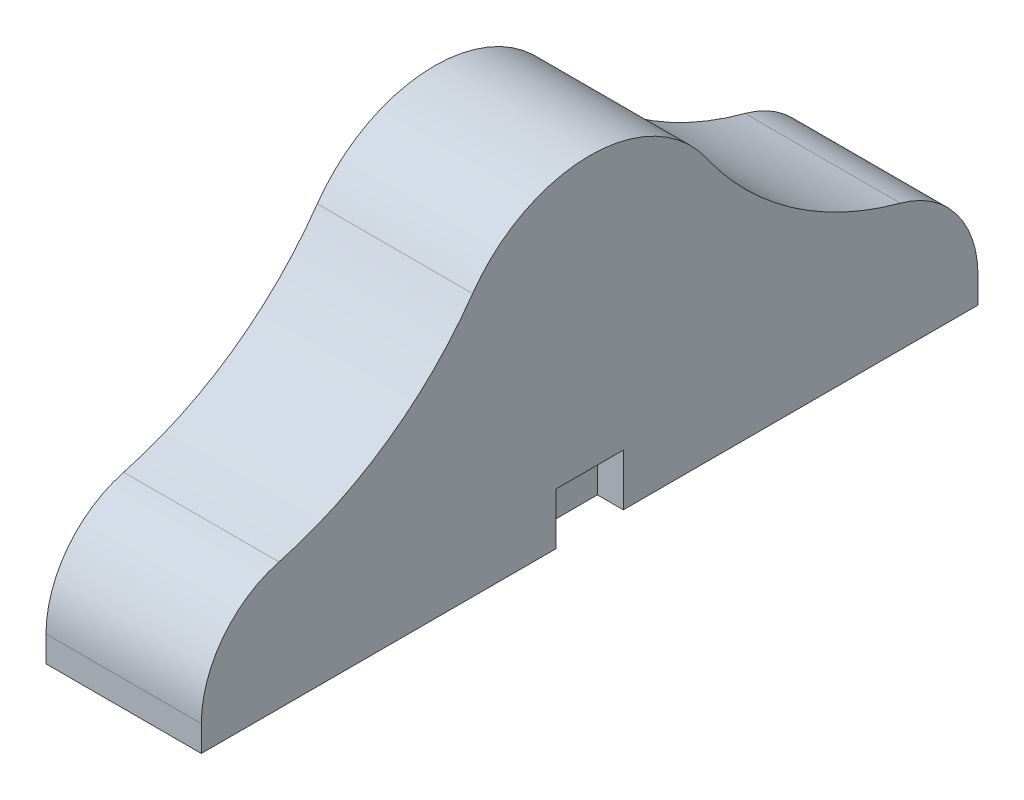
SolidWorks part; units mm, degrees
ref_plane "Front Plane" through (0, 0, 0) normal (0, 0, 1) x (1, 0, 0)
ref_plane "Top Plane" through (0, 0, 0) normal (0, 1, 0) x (1, 0, 0)
ref_plane "Right Plane" through (0, 0, 0) normal (1, 0, 0) x (0, 0, -1)
sketch "Sketch1" plane through (0, 0, 0) normal (1, 0, 0) x (0, 0, -1)
  line L0 (0, 0) -> (60, 0)
  line L1 (60, 0) -> (60, 2)
  line L2 (0, 0) -> (0, 2)
  line L3 (30, 0) -> (30, 27.8113) construction
  line L4 (30, 13.9616) -> (18.336, 22.1288) construction
  line L5 (-4.7429, 6.9408) -> (16.2966, 12.5783) construction
  line L6 (0, 2) -> (27.4, 2) construction
  line L7 (27.4, 2) -> (32.6, 2)
  line L8 (27.4, 2) -> (27.4, 4)
  line L9 (27.4, 4) -> (32.6, 4)
  line L10 (32.6, 2) -> (32.6, 4)
  arc A0 (20.9579, 20.293) -> (39.0421, 20.293) centre (30, 13.9616) cw
  arc A1 (0, 2) -> (6, 9.8194) centre (8.0952, 2) cw
  arc A2 (6, 9.8194) -> (20.9579, 20.293) centre (-0.9091, 35.6044) ccw
  arc A3 (60, 2) -> (54, 9.8194) centre (51.9048, 2) ccw
  arc A4 (54, 9.8194) -> (39.0421, 20.293) centre (60.9091, 35.6044) cw
  point P11 (30, 25)
  point P18 (30, 4)
  dimension "D1" = 55
  dimension "D2" = 15
  dimension "D3" = 60
  dimension "D4" = 2
  dimension "D5" = 6
  dimension "D6" = 25
  dimension "D7" = 5.2
  dimension "D8" = 2
extrude "Boss-Extrude1" add sketch "Sketch1" against normal blind 10
sketch "Sketch2" plane through (0, 0, 0) normal (1, 0, 0) x (0, 0, -1)
  line L0 (0, 0) -> (27.4, 0)
  line L1 (0, 0) -> (60, 0) construction
  line L2 (27.4, 0) -> (27.4, 4)
  line L3 (0, 2) -> (0, 0)
  line L4 (0, 0) -> (60, 0)
  line L5 (60, 0) -> (60, 2)
  line L6 (0, 2) -> (0, 0)
  line L8 (60, 0) -> (60, 2)
  line L9 (27.4, 4) -> (32.6, 4)
  line L10 (32.6, 4) -> (32.6, 0)
  line L11 (32.6, 0) -> (60, 0)
  arc A5 (60, 2) -> (54, 9.8194) centre (51.9048, 2) ccw
  arc A6 (39.0421, 20.293) -> (54, 9.8194) centre (60.9091, 35.6044) ccw
  arc A7 (39.0421, 20.293) -> (20.9579, 20.293) centre (30, 13.9616) ccw
  arc A8 (6, 9.8194) -> (20.9579, 20.293) centre (-0.9091, 35.6044) ccw
  arc A9 (6, 9.8194) -> (0, 2) centre (8.0952, 2) ccw
  arc A10 (60, 2) -> (54, 9.8194) centre (51.9048, 2) ccw
  arc A11 (39.0421, 20.293) -> (54, 9.8194) centre (60.9091, 35.6044) ccw
  arc A12 (39.0421, 20.293) -> (20.9579, 20.293) centre (30, 13.9616) ccw
  arc A13 (6, 9.8194) -> (20.9579, 20.293) centre (-0.9091, 35.6044) ccw
  arc A14 (6, 9.8194) -> (0, 2) centre (8.0952, 2) ccw
  dimension "D1" = 0
extrude "Boss-Extrude2" add sketch "Sketch2" along normal blind 2
